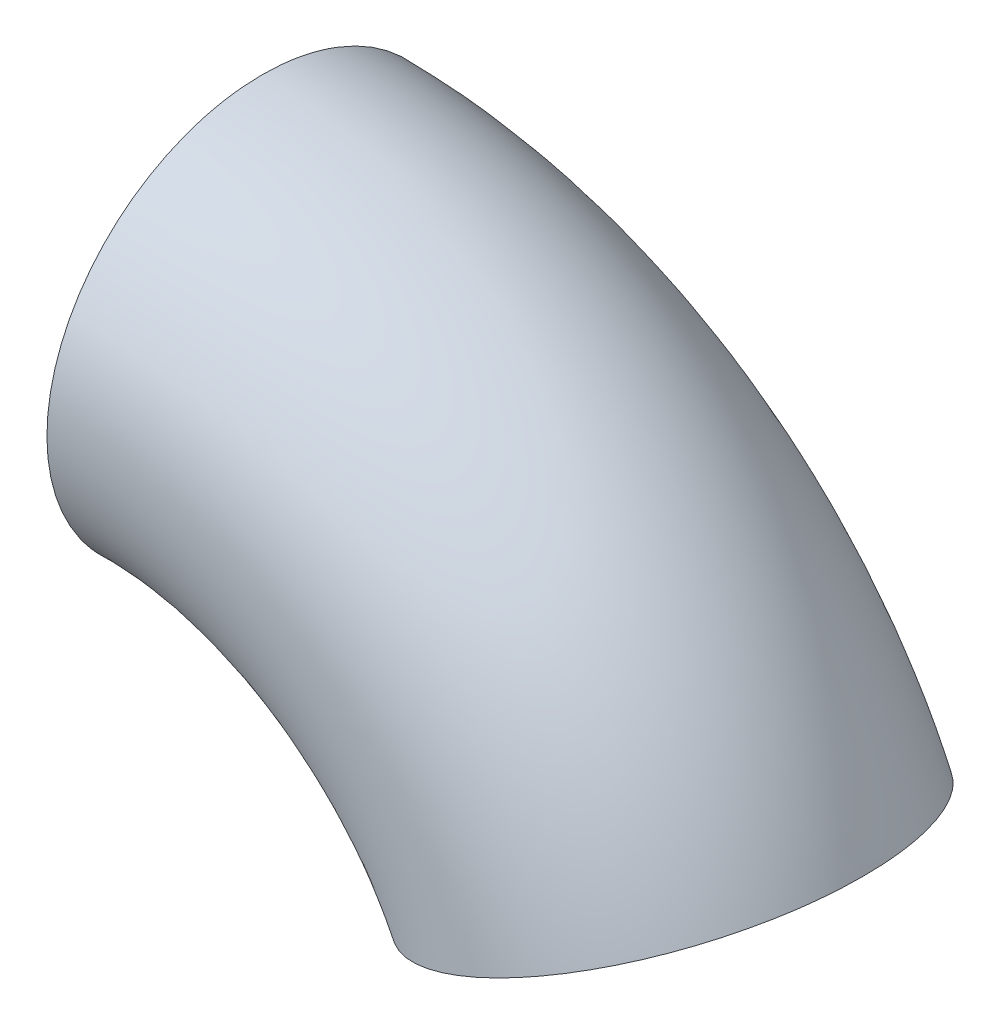
SolidWorks part; units mm, degrees
ref_plane "Front Plane" through (0, 0, 0) normal (0, 0, 1) x (1, 0, 0)
ref_plane "Top Plane" through (0, 0, 0) normal (0, 1, 0) x (1, 0, 0)
ref_plane "Right Plane" through (0, 0, 0) normal (1, 0, 0) x (0, 0, -1)
sketch "Sketch1" plane through (0, 0, 0) normal (0, 0, 1) x (1, 0, 0)
  line L1 (0, 0) -> (40.7596, -1.8116) construction
  arc A0 (0, 0) -> (40.7596, -25.9302) centre (0, -45) cw
ref_plane "Plane1" through (0, 0, 0) normal (0.999, -0.0444, 0) x (0, 0, -1)
sketch "Sketch2" plane through (0, 0, 0) normal (0.999, -0.0444, 0) x (0, 0, -1)
  circle A0 centre (0, 0) radius 20
  circle A1 centre (0, 0) radius 19.5
sweep "Sweep2" add profiles "Sketch2" path "Sketch1"
